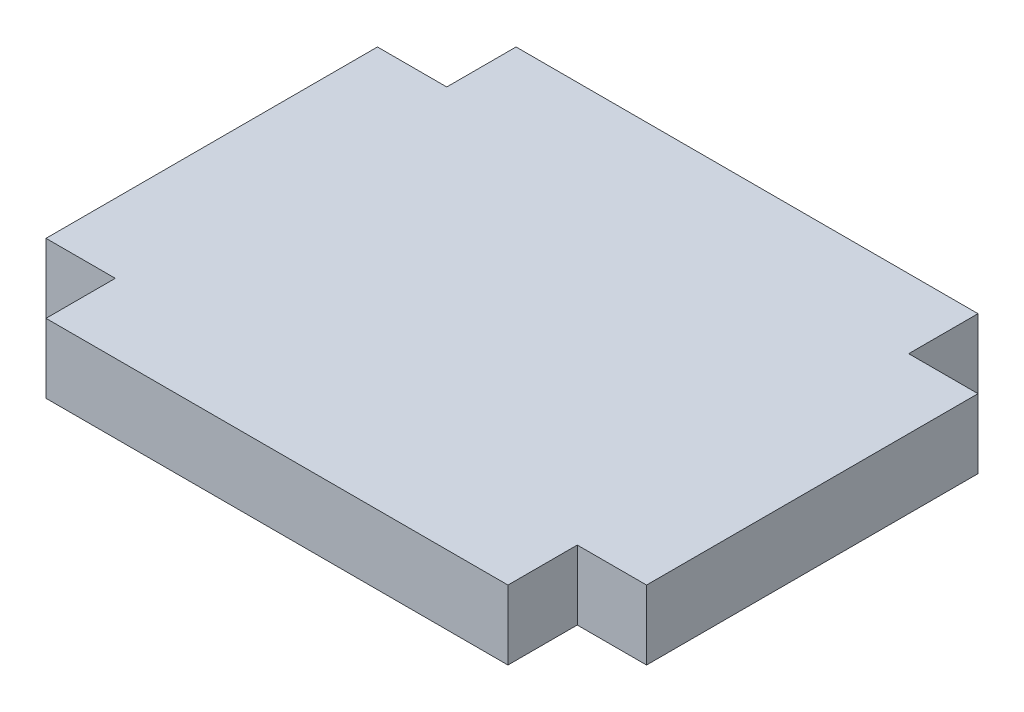
SolidWorks part; units mm, degrees
ref_plane "Front Plane" through (0, 0, 0) normal (0, 0, 1) x (1, 0, 0)
ref_plane "Top Plane" through (0, 0, 0) normal (0, 1, 0) x (1, 0, 0)
ref_plane "Right Plane" through (0, 0, 0) normal (1, 0, 0) x (0, 0, -1)
sketch "Sketch1" plane through (0, 0, 0) normal (0, 1, 0) x (1, 0, 0)
  line L0 (-10, 10.175) -> (10, 10.175)
  line L1 (10, 10.175) -> (10, 7.175)
  line L2 (10, 7.175) -> (13, 7.175)
  line L3 (13, 7.175) -> (13, -7.175)
  line L4 (13, -7.175) -> (10, -7.175)
  line L5 (10, -7.175) -> (10, -10.175)
  line L6 (10, -10.175) -> (-10, -10.175)
  line L7 (-10, -10.175) -> (-10, -7.175)
  line L8 (-10, -7.175) -> (-13, -7.175)
  line L9 (-13, -7.175) -> (-13, 7.175)
  line L10 (-13, 7.175) -> (-10, 7.175)
  line L11 (-10, 7.175) -> (-10, 10.175)
  point P2 (0, 10.175)
  point P13 (13, 0)
  dimension "D1" = 20
  dimension "D2" = 3
  dimension "D3" = 3
  dimension "D4" = 14.35
extrude "Boss-Extrude1" add sketch "Sketch1" along normal mid plane 3
